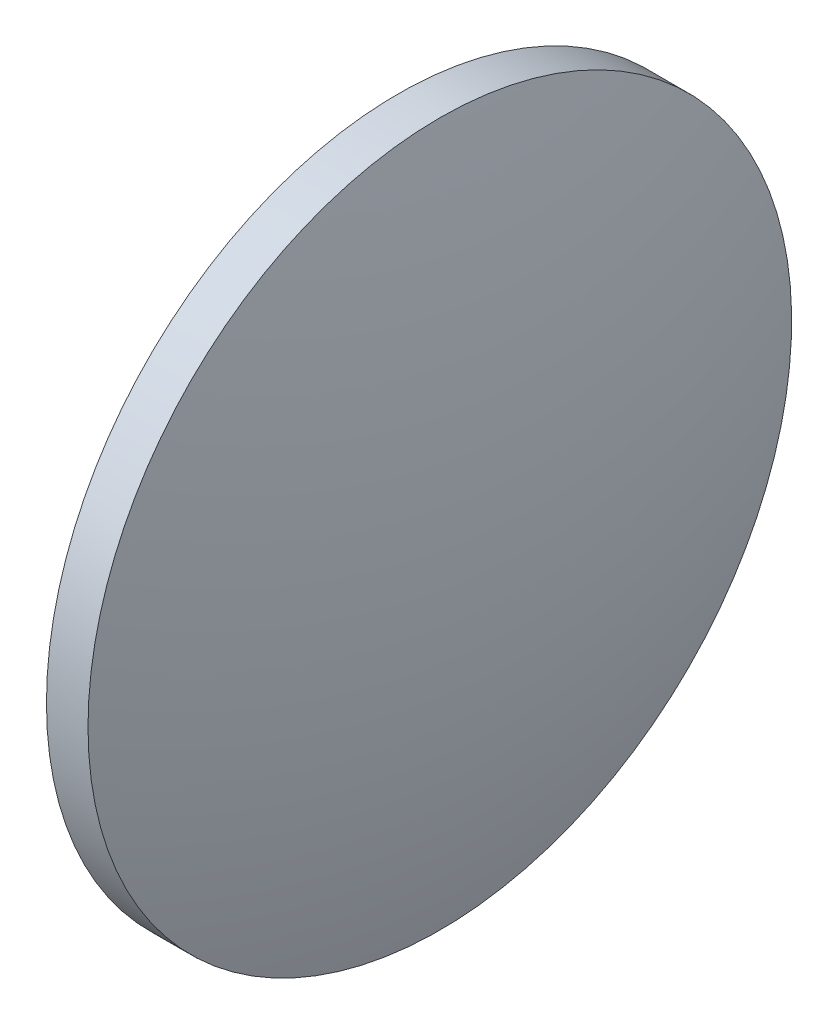
SolidWorks part; units mm, degrees
ref_plane "前视基准面" through (0, 0, 0) normal (0, 0, 1) x (1, 0, 0)
ref_plane "上视基准面" through (0, 0, 0) normal (0, 1, 0) x (1, 0, 0)
ref_plane "右视基准面" through (0, 0, 0) normal (1, 0, 0) x (0, 0, -1)
sketch "草图2" plane through (0, 0, 0) normal (0, 0, 1) x (1, 0, 0)
  line L0 (528.7585, 103.5178) -> (566.3505, 103.5178) construction
  line L1 (540.4486, 103.5178) -> (540.4486, 128.9178)
  line L2 (540.4486, 128.9178) -> (543.4486, 128.9178)
  line L3 (547.0486, 103.5178) -> (540.4486, 103.5178)
  arc A0 (547.0486, 103.5178) -> (543.4486, 128.9178) centre (455.643, 103.5178) ccw
revolve "旋转1" add sketch "草图2" angle 360 about L0
